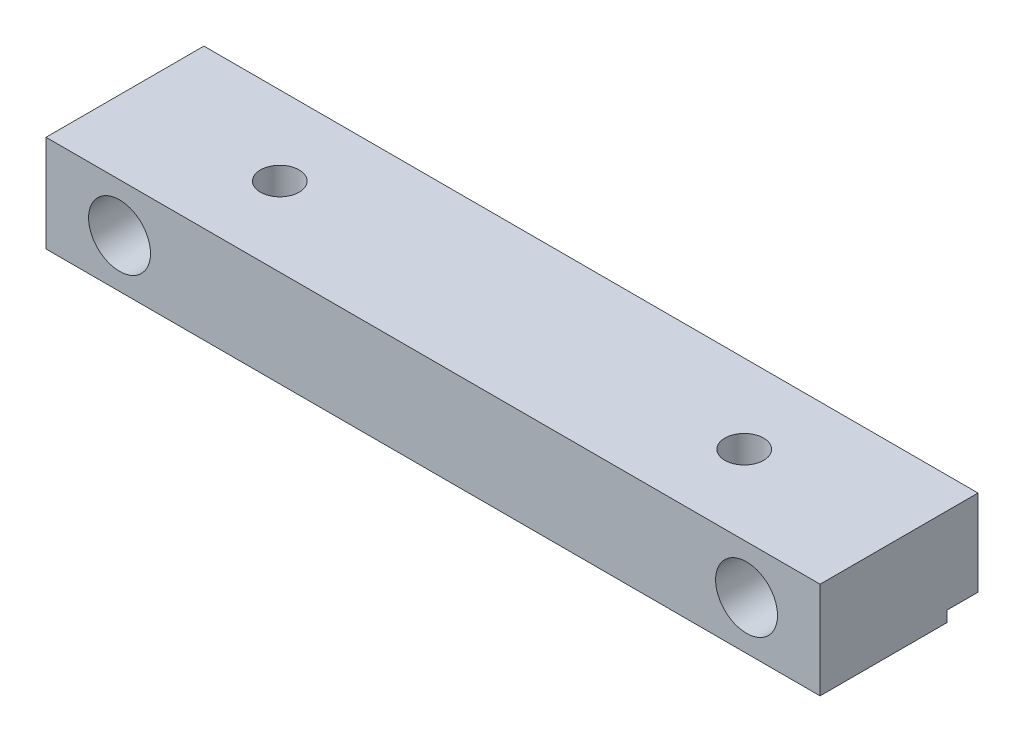
SolidWorks part; units mm, degrees
ref_plane "Front Plane" through (0, 0, 0) normal (0, 0, 1) x (1, 0, 0)
ref_plane "Top Plane" through (0, 0, 0) normal (0, 1, 0) x (1, 0, 0)
ref_plane "Right Plane" through (0, 0, 0) normal (1, 0, 0) x (0, 0, -1)
sketch "Sketch1" plane through (0, 0, 0) normal (0, 1, 0) x (1, 0, 0)
  line L1 (0, 0) -> (50, 0)
  line L2 (0, 0) -> (0, 10.2)
  line L3 (0, 10.2) -> (50, 10.2)
  line L4 (50, 0) -> (50, 10.2)
  dimension "D1" = 50
  dimension "D2" = 10.2
extrude "Boss-Extrude1" add sketch "Sketch1" along normal blind 6.25
hole_wizard "Ø4.0 (4) Diameter Hole1" positions "Sketch3" profile "Sketch2" hole size "Ø4.0" standard "Ansi Metric" end condition through all
sketch "Sketch3" plane through (0, 0, 0) normal (0, 0, 1) x (1, 0, 0)
  line L0 (0, 3.125) -> (4.75, 3.125) construction
  line L2 (4.75, 3.125) -> (45.25, 3.125) construction
  line L7 (0, 6.25) -> (0, 0) construction
  line L8 (0, 0) -> (50, 0) construction
  line L9 (45.25, 3.125) -> (50, 3.125) construction
  line L13 (50, 6.25) -> (50, 0) construction
  point P0 (4.75, 3.125)
  point P1 (45.25, 3.125)
  dimension "D2" = 40.5
sketch "Sketch2" plane through (4.75, 3.125, 0) normal (1, 0, 0) x (0, -1, 0)
  line L0 (0, 0) -> (0, 10.2)
  line L1 (0, 10.2) -> (2, 10.2)
  line L2 (2, 10.2) -> (2, 0)
  line L5 (2, 0) -> (0, 0)
  line L11 (0, -6.35) -> (0, 107.95) construction
  dimension "Thru Hole Dia." = 4
  dimension "Thru Hole Depth" = 10.2
ref_point "Point1"
ref_point "Point2"
hole_wizard "Ø2.5 (2.5) Diameter Hole1" positions "Sketch5" profile "Sketch4" hole size "Ø2.5" standard "Ansi Metric" end condition through all
sketch "Sketch5" plane through (0, 6.25, 0) normal (0, 1, 0) x (-1, 0, 0)
  line L0 (0, -5.1) -> (-10, -5.1) construction
  line L2 (-10, -5.1) -> (-40, -5.1) construction
  line L3 (-40, -5.1) -> (-50, -5.1) construction
  line L4 (0, -10.2) -> (0, 0) construction
  line L5 (-50, 0) -> (-50, -10.2) construction
  point P0 (-10, -5.1)
  point P1 (-40, -5.1)
  dimension "D1" = 30
sketch "Sketch4" plane through (10, 6.25, -5.1) normal (1, 0, 0) x (0, 0, 1)
  line L0 (0, 0) -> (0, 6.25)
  line L1 (0, 6.25) -> (1.25, 6.25)
  line L2 (1.25, 6.25) -> (1.25, 0)
  line L5 (1.25, 0) -> (0, 0)
  line L11 (0, -6.35) -> (0, 107.95) construction
  dimension "Thru Hole Dia." = 2.5
  dimension "Thru Hole Depth" = 6.25
sketch "Sketch6" plane through (50, 0, 0) normal (1, 0, 0) x (0, 0, -1)
  line L1 (10.2, 0) -> (8.2, 0)
  line L2 (10.2, 0) -> (10.2, 0.7)
  line L3 (10.2, 0.7) -> (8.2, 0.7)
  line L4 (8.2, 0) -> (8.2, 0.7)
  dimension "D1" = 0.7
  dimension "D2" = 2
extrude "Cut-Extrude1" cut sketch "Sketch6" against normal through all
